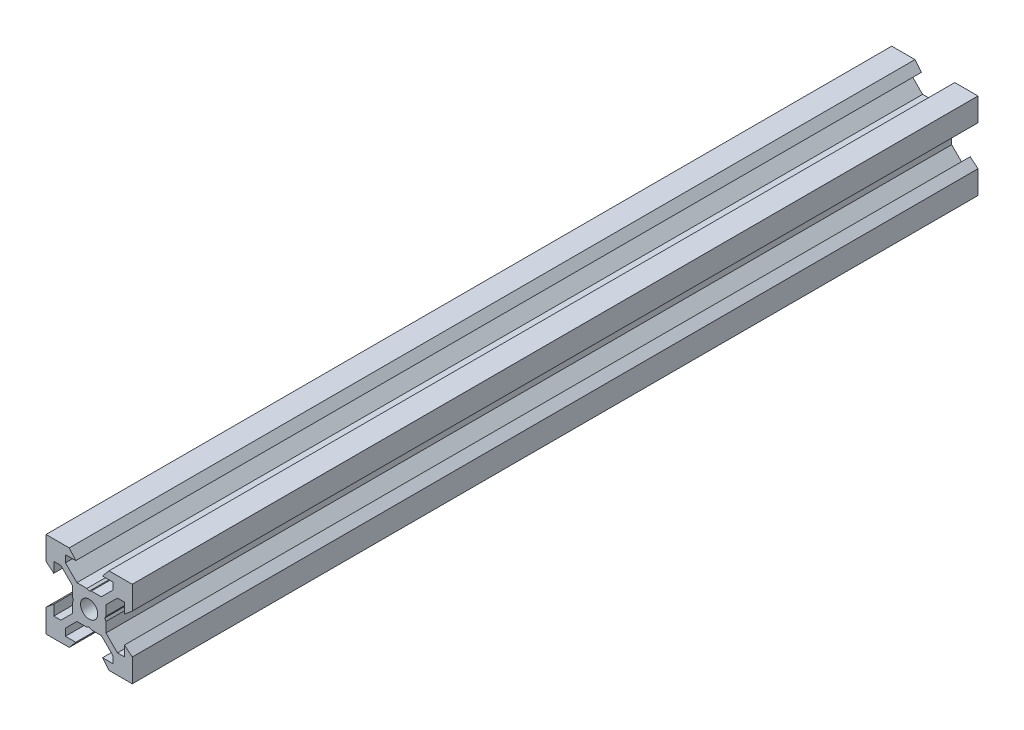
SolidWorks part; units mm, degrees
ref_plane "Front Plane" through (0, 0, 0) normal (0, 0, 1) x (1, 0, 0)
ref_plane "Top Plane" through (0, 0, 0) normal (0, 1, 0) x (1, 0, 0)
ref_plane "Right Plane" through (0, 0, 0) normal (1, 0, 0) x (0, 0, -1)
sketch "Sketch1" plane through (0, 0, 0) normal (0, 0, 1) x (1, 0, 0)
  line L0 (10, 10) -> (4.6104, 10) construction
  line L1 (10, 10) -> (10, 4.6104) construction
  line L2 (10, -10) -> (10, -4.6104) construction
  line L3 (10, -10) -> (4.6104, -10) construction
  line L4 (10, 10) -> (10, 4.6104)
  line L5 (6.5607, 5.5) -> (8.2, 5.5)
  line L6 (5.5, 8.2) -> (5.5, 6.5607)
  line L7 (10, 10) -> (4.6104, 10)
  line L8 (10, 10) -> (10, 4.6104)
  line L9 (6.5607, 5.5) -> (3.9, 2.8393)
  line L10 (5.5, 6.5607) -> (2.8393, 3.9)
  line L11 (10, 4.6104) -> (8.2, 3.1)
  line L12 (4.6104, 10) -> (3.1, 8.2)
  line L13 (8.2, 3.1) -> (8.2, 5.5)
  line L14 (3.1, 8.2) -> (5.5, 8.2)
  line L15 (-6.5607, 5.5) -> (-8.2, 5.5)
  line L16 (6.5607, -5.5) -> (8.2, -5.5)
  line L17 (3.1, -8.2) -> (5.5, -8.2)
  line L18 (8.2, -3.1) -> (8.2, -5.5)
  line L19 (4.6104, -10) -> (3.1, -8.2)
  line L20 (10, -4.6104) -> (8.2, -3.1)
  line L21 (0.5196, -3.9) -> (0, -3.6)
  line L22 (0.5196, 3.9) -> (0, 3.6)
  line L23 (3.6, 0) -> (3.9, -0.5196)
  line L24 (3.9, 0.5196) -> (3.6, 0)
  line L25 (3.9, 0.5196) -> (3.9, 2.8393)
  line L26 (2.8393, 3.9) -> (0.5196, 3.9)
  line L27 (3.9, -2.8393) -> (3.9, -0.5196)
  line L28 (2.8393, -3.9) -> (0.5196, -3.9)
  line L29 (5.5, -6.5607) -> (2.8393, -3.9)
  line L30 (6.5607, -5.5) -> (3.9, -2.8393)
  line L31 (10, -10) -> (10, -4.6104)
  line L32 (10, -10) -> (4.6104, -10)
  line L33 (5.5, -8.2) -> (5.5, -6.5607)
  line L34 (-6.5607, -5.5) -> (-8.2, -5.5)
  line L35 (10, -10) -> (10, -4.6104)
  line L36 (0, 0) -> (0, 8.2) construction
  line L37 (-10, -10) -> (-4.6104, -10) construction
  line L38 (-10, -10) -> (-10, -4.6104) construction
  line L39 (-10, 10) -> (-10, 4.6104) construction
  line L40 (-10, 10) -> (-4.6104, 10) construction
  line L41 (-10, -10) -> (-10, -4.6104)
  line L43 (-5.5, -8.2) -> (-5.5, -6.5607)
  line L44 (-10, -10) -> (-4.6104, -10)
  line L45 (-10, -10) -> (-10, -4.6104)
  line L46 (-6.5607, -5.5) -> (-3.9, -2.8393)
  line L47 (-5.5, -6.5607) -> (-2.8393, -3.9)
  line L48 (-2.8393, -3.9) -> (-0.5196, -3.9)
  line L49 (-3.9, -2.8393) -> (-3.9, -0.5196)
  line L50 (-2.8393, 3.9) -> (-0.5196, 3.9)
  line L51 (-3.9, 0.5196) -> (-3.9, 2.8393)
  line L52 (-3.9, 0.5196) -> (-3.6, 0)
  line L53 (-3.6, 0) -> (-3.9, -0.5196)
  line L54 (-0.5196, 3.9) -> (0, 3.6)
  line L55 (-0.5196, -3.9) -> (0, -3.6)
  line L56 (-10, -4.6104) -> (-8.2, -3.1)
  line L57 (-4.6104, -10) -> (-3.1, -8.2)
  line L58 (-8.2, -3.1) -> (-8.2, -5.5)
  line L59 (-3.1, -8.2) -> (-5.5, -8.2)
  line L60 (-10, -10) -> (10, -10) construction
  line L61 (-10, -10) -> (-10, 10) construction
  line L62 (-3.1, 8.2) -> (-5.5, 8.2)
  line L63 (-8.2, 3.1) -> (-8.2, 5.5)
  line L64 (-4.6104, 10) -> (-3.1, 8.2)
  line L65 (-10, 4.6104) -> (-8.2, 3.1)
  line L66 (-5.5, 6.5607) -> (-2.8393, 3.9)
  line L67 (-6.5607, 5.5) -> (-3.9, 2.8393)
  line L68 (-10, 10) -> (-10, 4.6104)
  line L69 (-10, 10) -> (-4.6104, 10)
  line L70 (-5.5, 8.2) -> (-5.5, 6.5607)
  line L71 (-10, 10) -> (10, 10) construction
  line L72 (-10, 10) -> (-10, 4.6104)
  line L73 (10, -10) -> (10, 10) construction
  line L74 (-10, -10) -> (10, 10) construction
  line L75 (-10, 10) -> (10, -10) construction
  circle A0 centre (0, 0) radius 2
  dimension "D7" = 4
  dimension "D1" = 20
  dimension "D2" = 5.3896
  dimension "D3" = 4.5
  dimension "D4" = 50
  dimension "D5" = 1.8
  dimension "D6" = 1.5104
  dimension "D8" = 5.5
  dimension "D9" = 120
  dimension "D10" = 0.3
  dimension "D11" = 2.3197
  dimension "D12" = 7.8
  dimension "D13" = 7.8
  dimension "D14" = 1.5
  dimension "D15" = 2.6607
extrude "Boss-Extrude1" add sketch "Sketch1" along normal blind 196.09 contours L70 L62 L64 L69 L68 L65 L63 L15 L67 L51 L52 L53 L49 L46 L34 L58 L56 L41 L44 L57 L59 L43 L47 L48 L55 L21 L28 L29 L33 L17 L19 L32 L31 L20 L18 L16 L30 L27 L23 L24 L25 L9 L5 L13 L11 L4 L7 L12 L14 L6 L10
